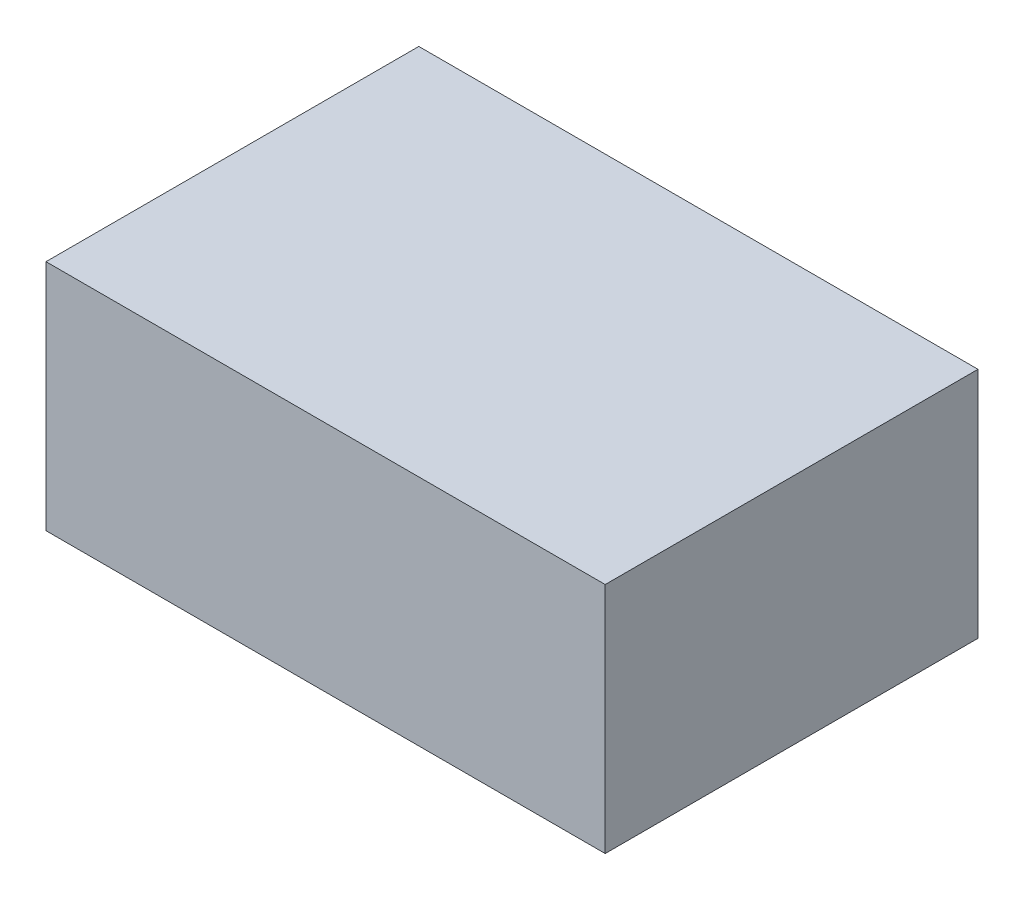
SolidWorks part; units mm, degrees
ref_plane "Front Plane" through (0, 0, 0) normal (0, 0, 1) x (1, 0, 0)
ref_plane "Top Plane" through (0, 0, 0) normal (0, 1, 0) x (1, 0, 0)
ref_plane "Right Plane" through (0, 0, 0) normal (1, 0, 0) x (0, 0, -1)
sketch "Sketch1" plane through (0, 0, 0) normal (0, 1, 0) x (1, 0, 0)
  line L0 (-152.4, 101.6) -> (152.4, -101.6) construction
  line L1 (-152.4, 101.6) -> (152.4, 101.6)
  line L2 (-152.4, 101.6) -> (-152.4, -101.6)
  line L3 (-152.4, -101.6) -> (152.4, -101.6)
  line L4 (152.4, 101.6) -> (152.4, -101.6)
  dimension "D1" = 203.2
  dimension "D2" = 304.8
extrude "Boss-Extrude1" add sketch "Sketch1" along normal mid plane 127
